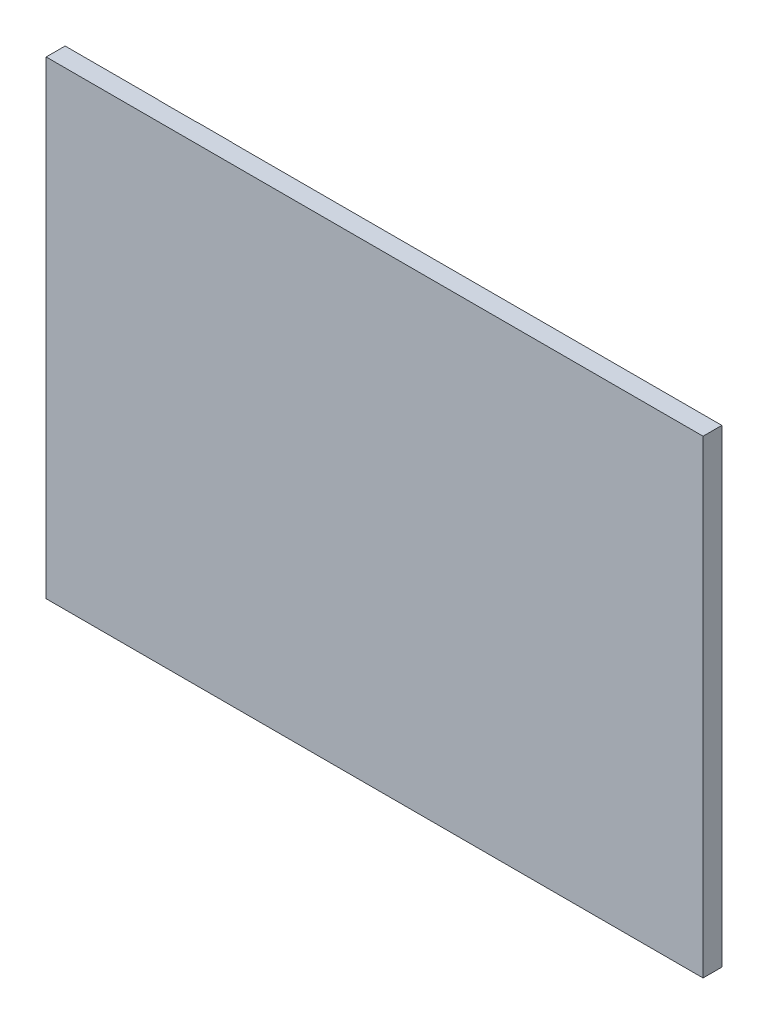
SolidWorks part; units mm, degrees
material "ABS"
ref_plane "Plano frontal" through (0, 0, 0) normal (0, 0, 1) x (1, 0, 0)
ref_plane "Plano superior" through (0, 0, 0) normal (0, 1, 0) x (1, 0, 0)
ref_plane "Plano direito" through (0, 0, 0) normal (1, 0, 0) x (0, 0, -1)
sketch "Esboço1" plane through (0, 0, 0) normal (0, 0, 1) x (1, 0, 0)
  line L1 (-175, 125) -> (175, 125)
  line L2 (-175, 125) -> (-175, -125)
  line L3 (-175, -125) -> (175, -125)
  line L4 (175, 125) -> (175, -125)
  line L5 (-175, 125) -> (175, -125) construction
  line L6 (-175, -125) -> (175, 125) construction
  point P0 (0, 0)
  dimension "D1" = 350
  dimension "D2" = 250
extrude "Ressalto-extrusão1" add sketch "Esboço1" along normal blind 10
sketch "Esboço2" plane through (0, 0, 0) normal (0, 0, -1) x (-1, 0, 0)
  line L0 (-175, 125) -> (175, 125) construction
  line L1 (175, -125) -> (125, -125)
  line L2 (175, -125) -> (175, 125)
  line L3 (175, 125) -> (125, 125)
  line L4 (125, -125) -> (125, 125)
  line L5 (175, -125) -> (-175, -125) construction
  line L6 (105, -125) -> (86, -125)
  line L7 (105, -125) -> (105, 125)
  line L8 (105, 125) -> (86, 125)
  line L9 (86, -125) -> (86, 125)
  dimension "D1" = 19
  dimension "D2" = 50
  dimension "D3" = 20
extrude "Ressalto-extrusão2" add sketch "Esboço2" along normal blind 0.1
